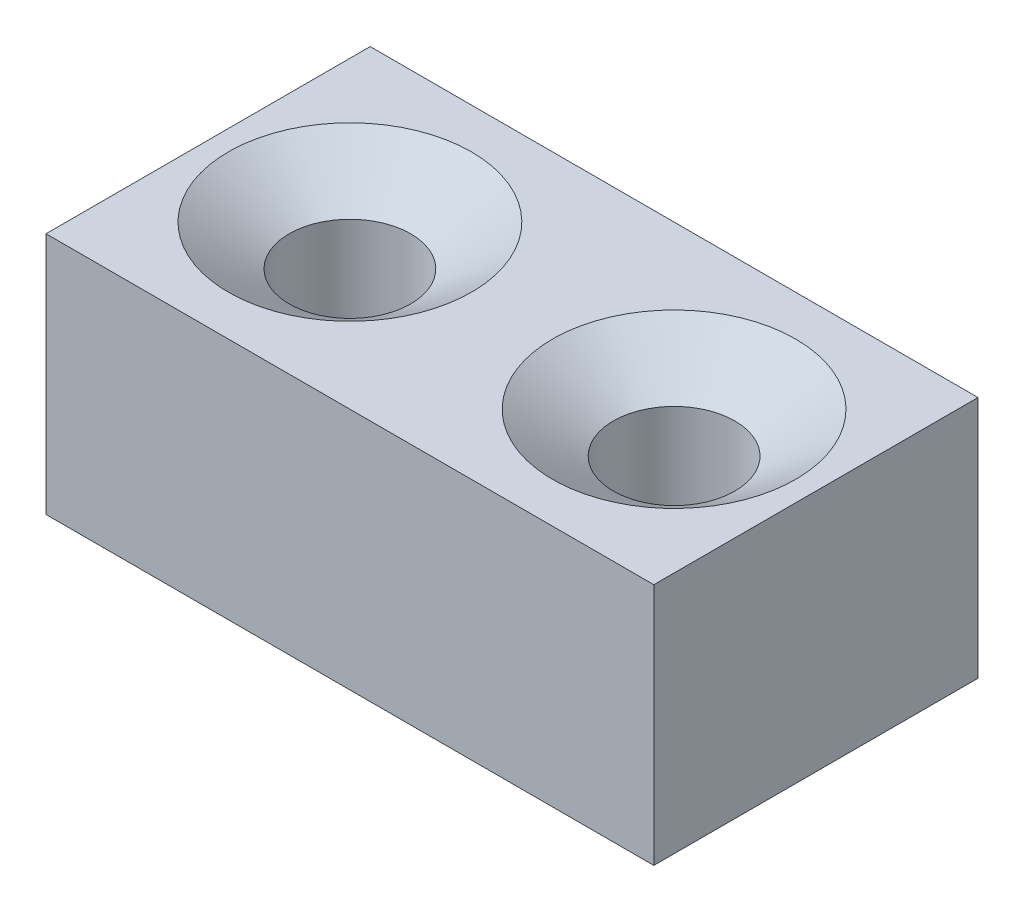
SolidWorks part; units mm, degrees
ref_plane "Front Plane" through (0, 0, 0) normal (0, 0, 1) x (1, 0, 0)
ref_plane "Top Plane" through (0, 0, 0) normal (0, 1, 0) x (1, 0, 0)
ref_plane "Right Plane" through (0, 0, 0) normal (1, 0, 0) x (0, 0, -1)
sketch "Sketch1" plane through (0, 0, 0) normal (0, 1, 0) x (1, 0, 0)
  line L1 (-75, -40) -> (75, -40)
  line L2 (-75, -40) -> (-75, 40)
  line L3 (-75, 40) -> (75, 40)
  line L4 (75, -40) -> (75, 40)
  line L5 (-75, -40) -> (75, 40) construction
  line L6 (-75, 40) -> (75, -40) construction
  point P0 (0, 0)
  dimension "D1" = 80
  dimension "D2" = 150
extrude "Boss-Extrude1" add sketch "Sketch1" along normal blind 60
sketch "Sketch2" plane through (0, 0, 0) normal (0, 0, 1) x (1, 0, 0)
  line L0 (0, 60) -> (-40, 60) construction
  line L1 (-75, 60) -> (75, 60) construction
  line L2 (-40, 60) -> (-70, 60)
  line L3 (-70, 60) -> (-55, 50)
  line L4 (-55, 50) -> (-55, 10)
  line L5 (-55, 10) -> (-40, 10)
  line L6 (-40, 10) -> (-40, 60)
  point P4 (-55, 70)
  point P9 (-60.5145, 80)
  dimension "D1" = 50
  dimension "D2" = 10
  dimension "D3" = 15
  dimension "D4" = 40
  dimension "D5" = 30
revolve "Cut-Revolve1" cut sketch "Sketch2" angle 360 about L6
mirror "Mirror1" about plane through (0, 0, 0) normal (1, 0, 0) of "Cut-Revolve1"
